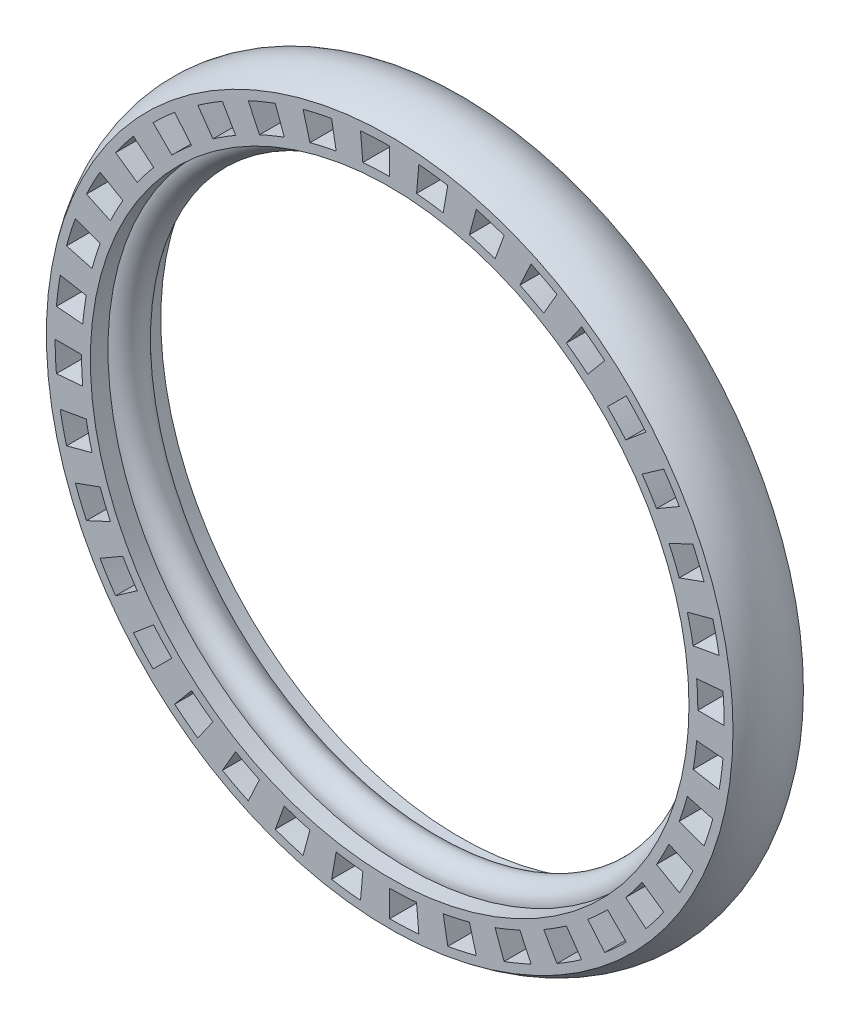
SolidWorks part; units mm, degrees
material "硅橡胶"
ref_plane "前视基准面" through (0, 0, 0) normal (0, 0, 1) x (1, 0, 0)
ref_plane "上视基准面" through (0, 0, 0) normal (0, 1, 0) x (1, 0, 0)
ref_plane "右视基准面" through (0, 0, 0) normal (1, 0, 0) x (0, 0, -1)
sketch "草图1" plane through (0, 0, 0) normal (0, 1, 0) x (1, 0, 0)
  line L0 (0, 0) -> (-43.398, 0) construction
  line L1 (0, 0) -> (0, 10.7341) construction
  line L2 (-34, 2) -> (-34, 4)
  line L3 (-34, 4) -> (-39, 4)
  line L4 (-34, -2) -> (-34, -4)
  line L5 (-34, -4) -> (-39, -4)
  arc A0 (-34, -2) -> (-34, 2) centre (-34, 0) ccw
  arc A1 (-39, 4) -> (-39, -4) centre (-34, 0) ccw
  point P10 (-43.398, 0)
  dimension "D1" = 4
  dimension "D4" = 5
  dimension "D2" = 34
  dimension "D3" = 2
revolve "旋转1" add sketch "草图1" angle 360 about L1
sketch "草图2" plane through (0, 0, -4) normal (0, 0, -1) x (-1, 0, 0)
  line L0 (0, 0) -> (0, 48.0881) construction
  line L1 (0, 35) -> (0, 38)
  line L2 (3.0505, 34.8668) -> (3.3119, 37.8554)
  line L3 (6.0777, 34.4683) -> (6.5986, 37.4227)
  line L4 (9.0587, 33.8074) -> (9.8351, 36.7052)
  line L5 (11.9707, 32.8892) -> (12.9968, 35.7083)
  line L6 (14.7916, 31.7208) -> (16.0595, 34.4397)
  line L7 (17.5, 30.3109) -> (19, 32.909)
  line L8 (20.0752, 28.6703) -> (21.7959, 31.1278)
  line L9 (22.4976, 26.8116) -> (24.4259, 29.1097)
  line L10 (24.7487, 24.7487) -> (26.8701, 26.8701)
  line L11 (26.8116, 22.4976) -> (29.1097, 24.4259)
  line L12 (28.6703, 20.0752) -> (31.1278, 21.7959)
  line L13 (30.3109, 17.5) -> (32.909, 19)
  line L14 (31.7208, 14.7916) -> (34.4397, 16.0595)
  line L15 (32.8892, 11.9707) -> (35.7083, 12.9968)
  line L16 (33.8074, 9.0587) -> (36.7052, 9.8351)
  line L17 (34.4683, 6.0777) -> (37.4227, 6.5986)
  line L18 (34.8668, 3.0505) -> (37.8554, 3.3119)
  line L19 (35, 0) -> (38, 0)
  line L20 (34.8668, -3.0505) -> (37.8554, -3.3119)
  line L21 (34.4683, -6.0777) -> (37.4227, -6.5986)
  line L22 (33.8074, -9.0587) -> (36.7052, -9.8351)
  line L23 (32.8892, -11.9707) -> (35.7083, -12.9968)
  line L24 (31.7208, -14.7916) -> (34.4397, -16.0595)
  line L25 (30.3109, -17.5) -> (32.909, -19)
  line L26 (28.6703, -20.0752) -> (31.1278, -21.7959)
  line L27 (26.8116, -22.4976) -> (29.1097, -24.4259)
  line L28 (24.7487, -24.7487) -> (26.8701, -26.8701)
  line L29 (22.4976, -26.8116) -> (24.4259, -29.1097)
  line L30 (20.0752, -28.6703) -> (21.7959, -31.1278)
  line L31 (17.5, -30.3109) -> (19, -32.909)
  line L32 (14.7916, -31.7208) -> (16.0595, -34.4397)
  line L33 (11.9707, -32.8892) -> (12.9968, -35.7083)
  line L34 (9.0587, -33.8074) -> (9.8351, -36.7052)
  line L35 (6.0777, -34.4683) -> (6.5986, -37.4227)
  line L36 (3.0505, -34.8668) -> (3.3119, -37.8554)
  line L37 (0, -35) -> (0, -38)
  line L38 (-3.0505, -34.8668) -> (-3.3119, -37.8554)
  line L39 (-6.0777, -34.4683) -> (-6.5986, -37.4227)
  line L40 (-9.0587, -33.8074) -> (-9.8351, -36.7052)
  line L41 (-11.9707, -32.8892) -> (-12.9968, -35.7083)
  line L42 (-14.7916, -31.7208) -> (-16.0595, -34.4397)
  line L43 (-17.5, -30.3109) -> (-19, -32.909)
  line L44 (-20.0752, -28.6703) -> (-21.7959, -31.1278)
  line L45 (-22.4976, -26.8116) -> (-24.4259, -29.1097)
  line L46 (-24.7487, -24.7487) -> (-26.8701, -26.8701)
  line L47 (-26.8116, -22.4976) -> (-29.1097, -24.4259)
  line L48 (-28.6703, -20.0752) -> (-31.1278, -21.7959)
  line L49 (-30.3109, -17.5) -> (-32.909, -19)
  line L50 (-31.7208, -14.7916) -> (-34.4397, -16.0595)
  line L51 (-32.8892, -11.9707) -> (-35.7083, -12.9968)
  line L52 (-33.8074, -9.0587) -> (-36.7052, -9.8351)
  line L53 (-34.4683, -6.0777) -> (-37.4227, -6.5986)
  line L54 (-34.8668, -3.0505) -> (-37.8554, -3.3119)
  line L55 (-35, 0) -> (-38, 0)
  line L56 (-34.8668, 3.0505) -> (-37.8554, 3.3119)
  line L57 (-34.4683, 6.0777) -> (-37.4227, 6.5986)
  line L58 (-33.8074, 9.0587) -> (-36.7052, 9.8351)
  line L59 (-32.8892, 11.9707) -> (-35.7083, 12.9968)
  line L60 (-31.7208, 14.7916) -> (-34.4397, 16.0595)
  line L61 (-30.3109, 17.5) -> (-32.909, 19)
  line L62 (-28.6703, 20.0752) -> (-31.1278, 21.7959)
  line L63 (-26.8116, 22.4976) -> (-29.1097, 24.4259)
  line L64 (-24.7487, 24.7487) -> (-26.8701, 26.8701)
  line L65 (-22.4976, 26.8116) -> (-24.4259, 29.1097)
  line L66 (-20.0752, 28.6703) -> (-21.7959, 31.1278)
  line L67 (-17.5, 30.3109) -> (-19, 32.909)
  line L68 (-14.7916, 31.7208) -> (-16.0595, 34.4397)
  line L69 (-11.9707, 32.8892) -> (-12.9968, 35.7083)
  line L70 (-9.0587, 33.8074) -> (-9.8351, 36.7052)
  line L71 (-6.0777, 34.4683) -> (-6.5986, 37.4227)
  line L72 (-3.0505, 34.8668) -> (-3.3119, 37.8554)
  arc A0 (3.0505, 34.8668) -> (0, 35) centre (0, 0) ccw
  arc A1 (3.3119, 37.8554) -> (0, 38) centre (0, 0) ccw
  arc A2 (9.0587, 33.8074) -> (6.0777, 34.4683) centre (0, 0) ccw
  arc A3 (9.8351, 36.7052) -> (6.5986, 37.4227) centre (0, 0) ccw
  arc A4 (14.7916, 31.7208) -> (11.9707, 32.8892) centre (0, 0) ccw
  arc A5 (16.0595, 34.4397) -> (12.9968, 35.7083) centre (0, 0) ccw
  arc A6 (20.0752, 28.6703) -> (17.5, 30.3109) centre (0, 0) ccw
  arc A7 (21.7959, 31.1278) -> (19, 32.909) centre (0, 0) ccw
  arc A8 (24.7487, 24.7487) -> (22.4976, 26.8116) centre (0, 0) ccw
  arc A9 (26.8701, 26.8701) -> (24.4259, 29.1097) centre (0, 0) ccw
  arc A10 (28.6703, 20.0752) -> (26.8116, 22.4976) centre (0, 0) ccw
  arc A11 (31.1278, 21.7959) -> (29.1097, 24.4259) centre (0, 0) ccw
  arc A12 (31.7208, 14.7916) -> (30.3109, 17.5) centre (0, 0) ccw
  arc A13 (34.4397, 16.0595) -> (32.909, 19) centre (0, 0) ccw
  arc A14 (33.8074, 9.0587) -> (32.8892, 11.9707) centre (0, 0) ccw
  arc A15 (36.7052, 9.8351) -> (35.7083, 12.9968) centre (0, 0) ccw
  arc A16 (34.8668, 3.0505) -> (34.4683, 6.0777) centre (0, 0) ccw
  arc A17 (37.8554, 3.3119) -> (37.4227, 6.5986) centre (0, 0) ccw
  arc A18 (34.8668, -3.0505) -> (35, 0) centre (0, 0) ccw
  arc A19 (37.8554, -3.3119) -> (38, 0) centre (0, 0) ccw
  arc A20 (33.8074, -9.0587) -> (34.4683, -6.0777) centre (0, 0) ccw
  arc A21 (36.7052, -9.8351) -> (37.4227, -6.5986) centre (0, 0) ccw
  arc A22 (31.7208, -14.7916) -> (32.8892, -11.9707) centre (0, 0) ccw
  arc A23 (34.4397, -16.0595) -> (35.7083, -12.9968) centre (0, 0) ccw
  arc A24 (28.6703, -20.0752) -> (30.3109, -17.5) centre (0, 0) ccw
  arc A25 (31.1278, -21.7959) -> (32.909, -19) centre (0, 0) ccw
  arc A26 (24.7487, -24.7487) -> (26.8116, -22.4976) centre (0, 0) ccw
  arc A27 (26.8701, -26.8701) -> (29.1097, -24.4259) centre (0, 0) ccw
  arc A28 (20.0752, -28.6703) -> (22.4976, -26.8116) centre (0, 0) ccw
  arc A29 (21.7959, -31.1278) -> (24.4259, -29.1097) centre (0, 0) ccw
  arc A30 (14.7916, -31.7208) -> (17.5, -30.3109) centre (0, 0) ccw
  arc A31 (16.0595, -34.4397) -> (19, -32.909) centre (0, 0) ccw
  arc A32 (9.0587, -33.8074) -> (11.9707, -32.8892) centre (0, 0) ccw
  arc A33 (9.8351, -36.7052) -> (12.9968, -35.7083) centre (0, 0) ccw
  arc A34 (3.0505, -34.8668) -> (6.0777, -34.4683) centre (0, 0) ccw
  arc A35 (3.3119, -37.8554) -> (6.5986, -37.4227) centre (0, 0) ccw
  arc A36 (-3.0505, -34.8668) -> (0, -35) centre (0, 0) ccw
  arc A37 (-3.3119, -37.8554) -> (0, -38) centre (0, 0) ccw
  arc A38 (-9.0587, -33.8074) -> (-6.0777, -34.4683) centre (0, 0) ccw
  arc A39 (-9.8351, -36.7052) -> (-6.5986, -37.4227) centre (0, 0) ccw
  arc A40 (-14.7916, -31.7208) -> (-11.9707, -32.8892) centre (0, 0) ccw
  arc A41 (-16.0595, -34.4397) -> (-12.9968, -35.7083) centre (0, 0) ccw
  arc A42 (-20.0752, -28.6703) -> (-17.5, -30.3109) centre (0, 0) ccw
  arc A43 (-21.7959, -31.1278) -> (-19, -32.909) centre (0, 0) ccw
  arc A44 (-24.7487, -24.7487) -> (-22.4976, -26.8116) centre (0, 0) ccw
  arc A45 (-26.8701, -26.8701) -> (-24.4259, -29.1097) centre (0, 0) ccw
  arc A46 (-28.6703, -20.0752) -> (-26.8116, -22.4976) centre (0, 0) ccw
  arc A47 (-31.1278, -21.7959) -> (-29.1097, -24.4259) centre (0, 0) ccw
  arc A48 (-31.7208, -14.7916) -> (-30.3109, -17.5) centre (0, 0) ccw
  arc A49 (-34.4397, -16.0595) -> (-32.909, -19) centre (0, 0) ccw
  arc A50 (-33.8074, -9.0587) -> (-32.8892, -11.9707) centre (0, 0) ccw
  arc A51 (-36.7052, -9.8351) -> (-35.7083, -12.9968) centre (0, 0) ccw
  arc A52 (-34.8668, -3.0505) -> (-34.4683, -6.0777) centre (0, 0) ccw
  arc A53 (-37.8554, -3.3119) -> (-37.4227, -6.5986) centre (0, 0) ccw
  arc A54 (-34.8668, 3.0505) -> (-35, 0) centre (0, 0) ccw
  arc A55 (-37.8554, 3.3119) -> (-38, 0) centre (0, 0) ccw
  arc A56 (-33.8074, 9.0587) -> (-34.4683, 6.0777) centre (0, 0) ccw
  arc A57 (-36.7052, 9.8351) -> (-37.4227, 6.5986) centre (0, 0) ccw
  arc A58 (-31.7208, 14.7916) -> (-32.8892, 11.9707) centre (0, 0) ccw
  arc A59 (-34.4397, 16.0595) -> (-35.7083, 12.9968) centre (0, 0) ccw
  arc A60 (-28.6703, 20.0752) -> (-30.3109, 17.5) centre (0, 0) ccw
  arc A61 (-31.1278, 21.7959) -> (-32.909, 19) centre (0, 0) ccw
  arc A62 (-24.7487, 24.7487) -> (-26.8116, 22.4976) centre (0, 0) ccw
  arc A63 (-26.8701, 26.8701) -> (-29.1097, 24.4259) centre (0, 0) ccw
  arc A64 (-20.0752, 28.6703) -> (-22.4976, 26.8116) centre (0, 0) ccw
  arc A65 (-21.7959, 31.1278) -> (-24.4259, 29.1097) centre (0, 0) ccw
  arc A66 (-14.7916, 31.7208) -> (-17.5, 30.3109) centre (0, 0) ccw
  arc A67 (-16.0595, 34.4397) -> (-19, 32.909) centre (0, 0) ccw
  arc A68 (-9.0587, 33.8074) -> (-11.9707, 32.8892) centre (0, 0) ccw
  arc A69 (-9.8351, 36.7052) -> (-12.9968, 35.7083) centre (0, 0) ccw
  arc A70 (-3.0505, 34.8668) -> (-6.0777, 34.4683) centre (0, 0) ccw
  arc A71 (-3.3119, 37.8554) -> (-6.5986, 37.4227) centre (0, 0) ccw
  dimension "D1" = 5
  dimension "D2" = 38
  dimension "D3" = 35
  dimension "D4" = 36
extrude "切除-拉伸1" cut sketch "草图2" against normal up to next (8 mm away)
